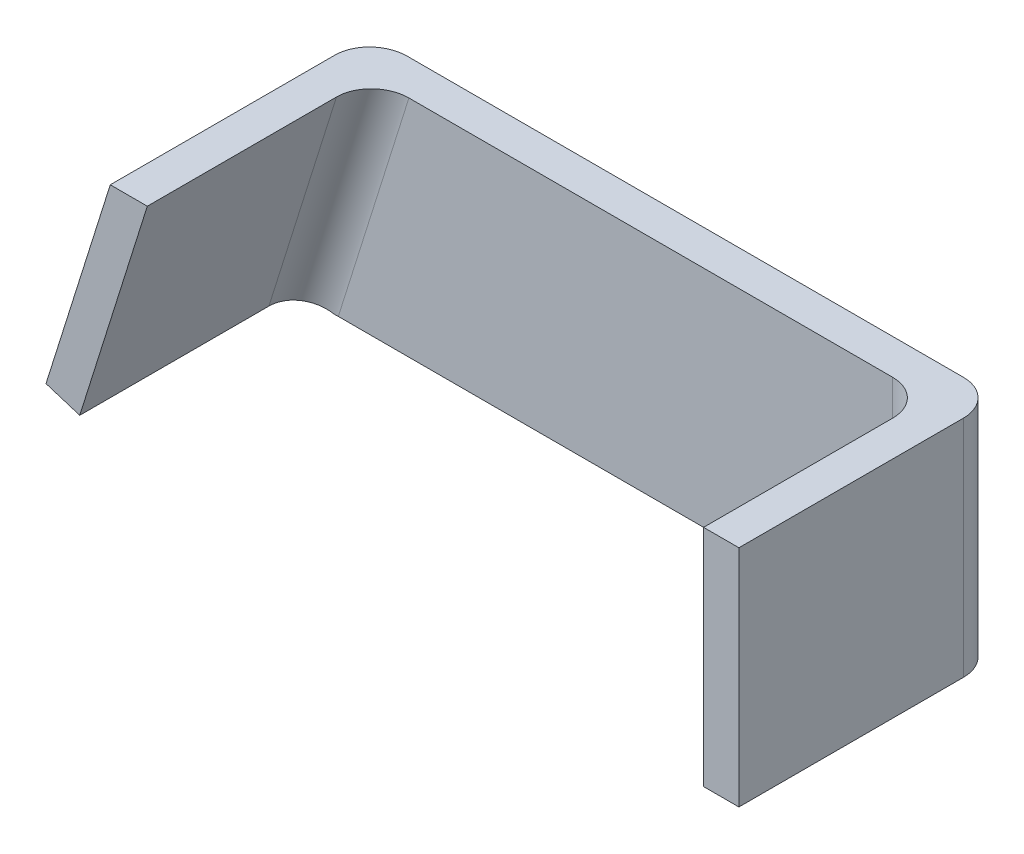
SolidWorks part; units mm, degrees
material "PE High Density"
ref_plane "Front Plane" through (0, 0, 0) normal (0, 0, 1) x (1, 0, 0)
ref_plane "Top Plane" through (0, 0, 0) normal (0, 1, 0) x (1, 0, 0)
ref_plane "Right Plane" through (0, 0, 0) normal (1, 0, 0) x (0, 0, -1)
sketch "Sketch1" plane through (0, 0, 0) normal (0, 0, 1) x (1, 0, 0)
  line L1 (-44.433, 15.875) -> (44.467, 15.875)
  line L3 (-44.433, -15.875) -> (44.467, -15.875)
  line L10 (-44.433, 15.875) -> (-53.5192, -13.0175)
  line L12 (0.017, -15.875) -> (0.017, 75.0464) construction
  line L13 (0.017, -15.875) -> (147.1451, -15.875) construction
  line L15 (44.467, 15.875) -> (44.467, -15.875)
  line L17 (-44.433, -15.875) -> (-53.5192, -13.0175)
extrude "Boss-Extrude1" add sketch "Sketch1" along normal blind 5
sketch "Sketch2" plane through (0, 0, 5) normal (0, 0, 1) x (1, 0, 0)
  line L1 (44.467, 15.875) -> (-44.433, 15.875) construction
  line L2 (-48.7495, -14.5175) -> (-53.5192, -13.0175)
  line L3 (39.467, -15.875) -> (39.467, 15.875)
  line L4 (-44.433, -15.875) -> (44.467, -15.875) construction
  line L5 (44.467, -15.875) -> (44.467, 15.875) construction
  line L9 (39.467, 15.875) -> (44.467, 15.875)
  line L10 (44.467, 15.875) -> (44.467, -15.875)
  line L11 (44.467, -15.875) -> (39.467, -15.875)
  line L12 (-48.7495, -14.5175) -> (-39.1915, 15.875)
  line L13 (-53.5192, -13.0175) -> (-44.433, 15.875)
  line L14 (-44.433, 15.875) -> (-39.1915, 15.875)
  line L15 (-44.433, 15.875) -> (-53.5192, -13.0175) construction
  dimension "D1" = 5
  dimension "D2" = 5
extrude "Boss-Extrude2" add sketch "Sketch2" along normal blind 31.75
fillet "Fillet1" radius 5 1 edges at (-48.9761, 1.4287, 0)
fillet "Fillet4" radius 5 3 edges at (44.467, 0, 0) (39.467, 0, 5) (-43.9705, 0.6787, 5)
equation "\"Plate Screw Hole Diameter\"= 0.116in"
equation "\"Plate Width\" = 3.5in"
equation "\"Plate Thickness\" = 0.375in"
equation "\"Num holes\" = 4"
equation "\"Plate Height\" = 1.25in"
equation "\"D1@Sketch11\"=\"Plate Width\" / ( \"Num holes\" + 1)"
equation "\"D2@Sketch11\"=\"Plate Thickness\"/2"
equation "\"D3@LPattern1\"=\"Plate Width\" / ( \"Num holes\"  + 1 )"
equation "\"Top Plate Width\" = 4.5in"
equation "\"Plate Clearance Hole Diameter\" = 0.125in"
equation "\"Plate Tap Hole Diameter\" = 0.116in"
equation "\"Bottom Plate Length\" = 6.5in"
equation "\"Number Eight Clearance Size\" = 0.177in"
equation "\"back_brace_height_offset\"=0.35"
equation "\"D2@Sketch13\"=\"Plate Tap Hole Diameter\""
